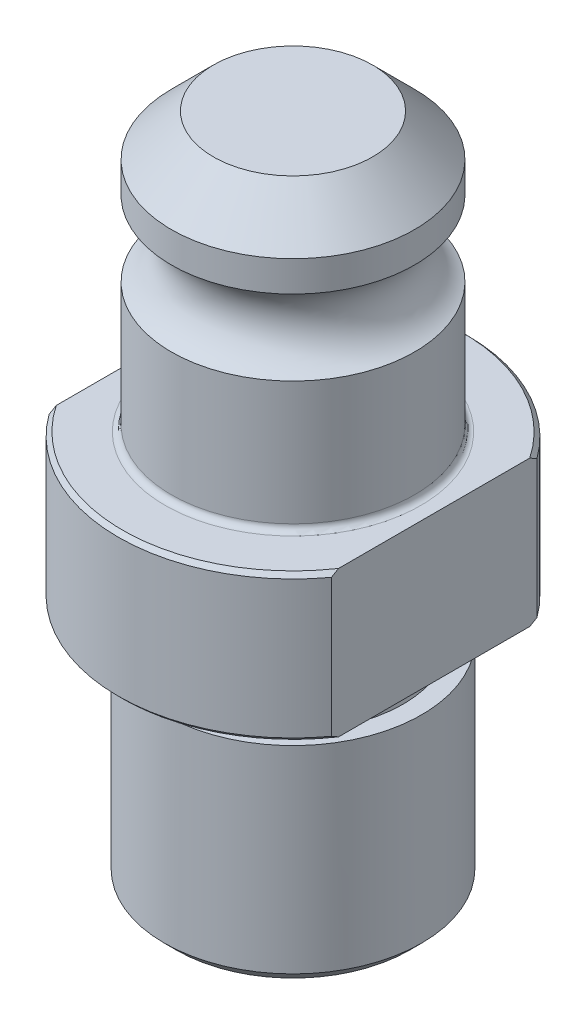
SolidWorks part; units mm, degrees
ref_plane "Front Plane" through (0, 0, 0) normal (0, 0, 1) x (1, 0, 0)
ref_plane "Top Plane" through (0, 0, 0) normal (0, 1, 0) x (1, 0, 0)
ref_plane "Right Plane" through (0, 0, 0) normal (1, 0, 0) x (0, 0, -1)
sketch "Sketch1" plane through (0, 0, 0) normal (0, 0, 1) x (1, 0, 0)
  line L0 (0, 52.2986) -> (0, -30.2514)
  line L1 (0, -30.2514) -> (-15.875, -30.2514)
  line L2 (-15.875, -30.2514) -> (-15.875, -4.318)
  line L3 (-15.875, -4.318) -> (-13.6017, -4.318)
  line L4 (-13.6017, -4.318) -> (-13.6017, -1.27)
  line L5 (-14.8717, 0) -> (-21.5519, 0)
  line L6 (-21.5519, 0) -> (-21.5519, 18.0086)
  line L7 (-21.5519, 18.0086) -> (-15.0114, 18.0086)
  line L8 (-15.0114, 18.0086) -> (-15.0114, 34.036)
  line L9 (-15.0114, 47.117) -> (-9.8298, 52.2986)
  line L10 (-9.8298, 52.2986) -> (0, 52.2986)
  line L11 (0, -30.2514) -> (0, -73.6863) construction
  line L12 (-15.0114, 43.3324) -> (-15.0114, 47.117)
  arc A0 (-15.0114, 34.036) -> (-15.0114, 43.3324) centre (-16.9897, 38.6842) ccw
  arc A1 (-14.8717, 0) -> (-13.6017, -1.27) centre (-14.8717, -1.27) cw
  dimension "D13" = 23.876
  dimension "D14" = 1.27
  dimension "D15" = 5.0517
  dimension "D1" = 31.75
  dimension "D2" = 27.2034
  dimension "D3" = 43.1038
  dimension "D4" = 30.0228
  dimension "D5" = 30.2514
  dimension "D6" = 18.0086
  dimension "D7" = 4.318
  dimension "D8" = 45
  dimension "D9" = 19.6596
  dimension "D10" = 34.29
  dimension "D11" = 16.0274
  dimension "D12" = 9.2964
revolve "Revolve1" add sketch "Sketch1" angle 360 about L11
chamfer "Chamfer1" distance 0.508 angle 45 2 edges at (-21.5519, 0, 0) (-21.5519, 18.0086, 0)
chamfer "Chamfer2" distance 1.524 angle 45 1 edges at (-15.875, -30.2514, 0)
sketch "Sketch2" plane through (0, 18.0086, 0) normal (0, 1, 0) x (1, 0, 0)
  line L0 (-17.4244, 12.6836) -> (-17.4244, -12.6836)
  line L1 (17.4244, 12.6836) -> (17.4244, -12.6836)
  circle A0 centre (0, 0) radius 21.5519 construction
  arc A1 (17.4244, -12.6836) -> (17.4244, 12.6836) centre (0, 0) ccw
  arc A2 (-17.4244, 12.6836) -> (-17.4244, -12.6836) centre (0, 0) ccw
  dimension "D1" = 17.4244
  dimension "D2" = 17.4244
extrude "Cut-Extrude1" cut sketch "Sketch2" against normal through all
fillet "Fillet1" radius 0.762 1 edges at (-15.0114, 18.0086, 0)
